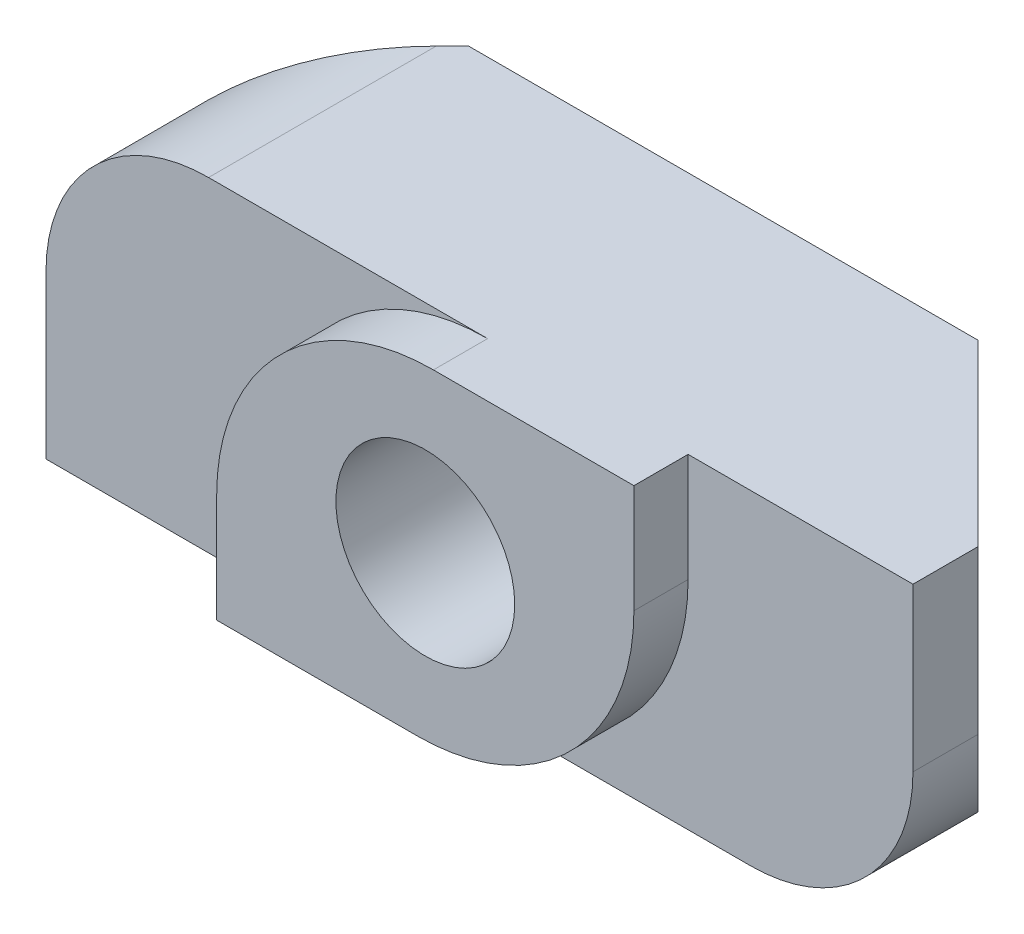
SolidWorks part; units mm, degrees
ref_plane "Front Plane" through (0, 0, 0) normal (0, 0, 1) x (1, 0, 0)
ref_plane "Top Plane" through (0, 0, 0) normal (0, 1, 0) x (1, 0, 0)
ref_plane "Right Plane" through (0, 0, 0) normal (1, 0, 0) x (0, 0, -1)
sketch "Sketch1" plane through (0, 0, 0) normal (0, 1, 0) x (1, 0, 0)
  line L0 (4.7, 0) -> (-4.7, 0)
  line L1 (-4.7, 0) -> (-8, -3.3)
  line L2 (-8, -3.3) -> (-8, -4.5)
  line L3 (-8, -4.5) -> (-3.85, -4.5)
  line L4 (-3.85, -4.5) -> (-3.85, -5.5)
  line L5 (-3.85, -5.5) -> (3.85, -5.5)
  line L6 (0, -5.5) -> (0, 0) construction
  line L7 (3.85, -4.5) -> (3.85, -5.5)
  line L8 (8, -4.5) -> (3.85, -4.5)
  line L9 (8, -3.3) -> (8, -4.5)
  line L10 (4.7, 0) -> (8, -3.3)
  line L11 (-3.85, -4.5) -> (3.85, -4.5) construction
  dimension "D1" = 3.85
  dimension "D2" = 1
  dimension "D3" = 45
  dimension "D4" = 8
  dimension "D5" = 4.5
  dimension "D6" = 1.2
extrude "Boss-Extrude1" add sketch "Sketch1" along normal blind 6
sketch "Sketch2" plane through (0, 0, 5.5) normal (0, 0, 1) x (1, 0, 0)
  line L0 (0, 0) -> (0, 6) construction
  line L1 (-3.85, 6) -> (3.85, 6) construction
  circle A0 centre (0, 3) radius 1.65
  dimension "D1" = 3.3
extrude "Cut-Extrude1" cut sketch "Sketch2" against normal through all
fillet "Fillet1" radius 4 2 edges at (-3.85, 6, 5) (3.85, 0, 5)
fillet "Fillet2" radius 3 2 edges at (-8, 6, 3.9) (8, 0, 3.9)
